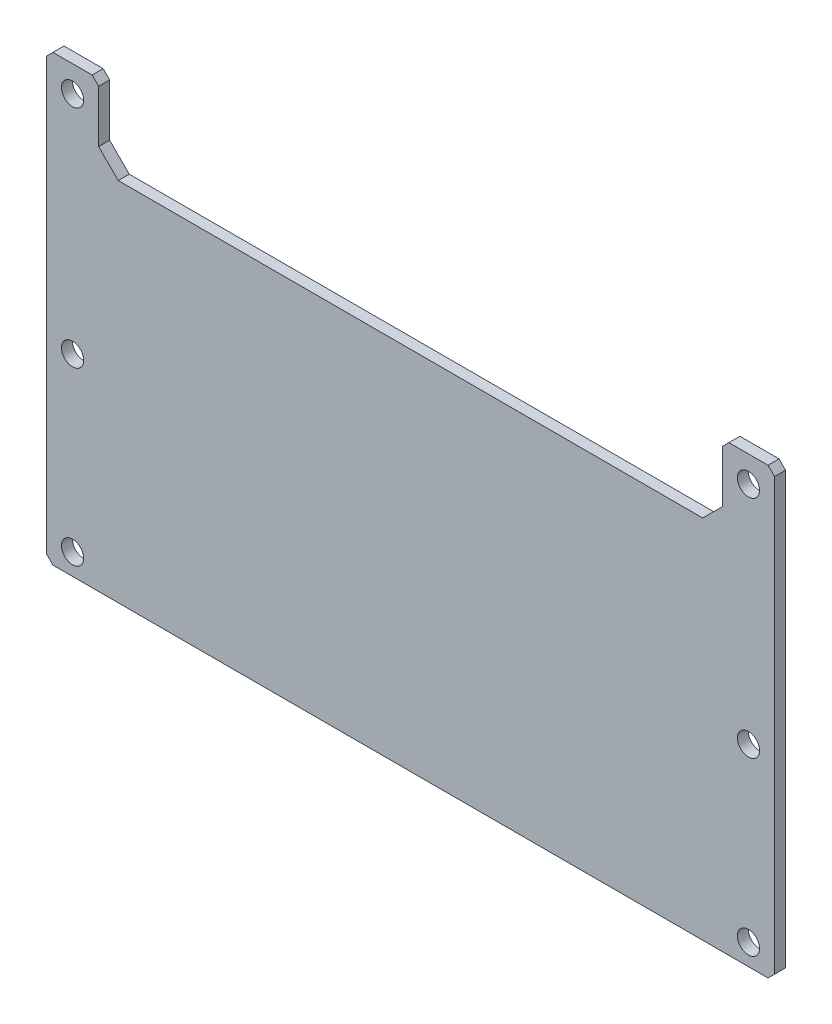
SolidWorks part; units mm, degrees
ref_plane "Front Plane" through (0, 0, 0) normal (0, 0, 1) x (1, 0, 0)
ref_plane "Top Plane" through (0, 0, 0) normal (0, 1, 0) x (1, 0, 0)
ref_plane "Right Plane" through (0, 0, 0) normal (1, 0, 0) x (0, 0, -1)
sketch "Sketch1" plane through (0, 0, 0) normal (0, 0, 1) x (1, 0, 0)
  line L0 (0, 1) -> (1, 0)
  line L1 (1, 0) -> (110.5, 0)
  line L2 (110.5, 0) -> (111.5, 1)
  line L3 (111.5, 1) -> (111.5, 67)
  line L4 (111.5, 67) -> (110.5, 68)
  line L5 (110.5, 68) -> (104.5, 68)
  line L6 (104.5, 68) -> (103.5, 67)
  line L7 (103.5, 67) -> (103.5, 59)
  line L8 (103.5, 59) -> (100.5, 56)
  line L9 (100.5, 56) -> (11, 56)
  line L10 (11, 56) -> (8, 59)
  line L11 (8, 59) -> (8, 67)
  line L12 (8, 67) -> (7, 68)
  line L13 (7, 68) -> (1, 68)
  line L14 (1, 68) -> (0, 67)
  line L15 (0, 67) -> (0, 1)
  line L16 (0, 29.5) -> (111.5, 29.5) construction
  line L17 (0, 3.25) -> (111.5, 3.25) construction
  line L18 (0, 64) -> (111.5, 64) construction
  line L19 (4, 0) -> (4, 68) construction
  line L20 (107.5, 0) -> (107.5, 68) construction
  circle A0 centre (107.5, 29.5) radius 1.7
  circle A1 centre (107.5, 64) radius 1.7
  circle A2 centre (107.5, 3.25) radius 1.7
  circle A3 centre (4, 64) radius 1.7
  circle A4 centre (4, 29.5) radius 1.7
  circle A5 centre (4, 3.25) radius 1.7
extrude "Boss-Extrude1" add sketch "Sketch1" along normal blind 1.6866
